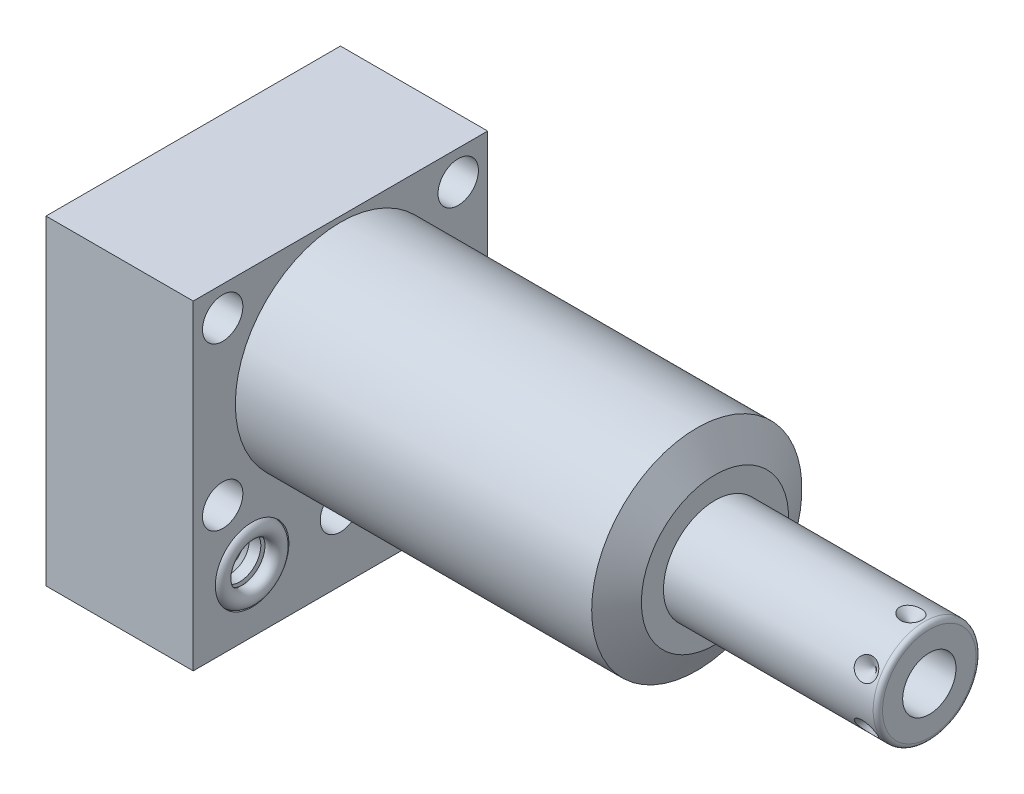
SolidWorks part; units mm, degrees
material "Alloy Steel"
ref_plane "Front Plane" through (0, 0, 0) normal (0, 0, 1) x (1, 0, 0)
ref_plane "Top Plane" through (0, 0, 0) normal (0, 1, 0) x (1, 0, 0)
ref_plane "Right Plane" through (0, 0, 0) normal (1, 0, 0) x (0, 0, -1)
ref_plane "Plane1" through (0, 0, 0) normal (1, 0, 0) x (0, 0, -1)
sketch "Sketch1" plane through (0, 0, 0) normal (1, 0, 0) x (0, 0, -1)
  line L0 (-31.75, 23.8252) -> (-31.75, -45.2628)
  line L1 (-31.75, -45.2628) -> (31.75, -45.2628)
  line L2 (31.75, -45.2628) -> (31.75, 23.8252)
  line L3 (31.75, 23.8252) -> (-31.75, 23.8252)
  line L4 (0, -55.6514) -> (0, 27.6098) construction
  dimension "D1" = 63.5
  dimension "D2" = 69.088
  dimension "D3" = 23.8252
extrude "Extrude1" add sketch "Sketch1" along normal blind 80.772 and the other way blind 31.75
ref_plane "Plane2" through (0, 0, 0) normal (1, 0, 0) x (0, 0, -1)
sketch "Sketch2" plane through (0, 0, 0) normal (1, 0, 0) x (0, 0, -1)
  line L0 (-26.0541, 0) -> (26.0541, 0) construction
  line L5 (31.75, 23.8252) -> (-31.75, 23.8252)
  line L6 (-31.75, 23.8252) -> (-31.75, -45.2628)
  line L7 (-31.75, -45.2628) -> (31.75, -45.2628)
  line L8 (31.75, -45.2628) -> (31.75, 23.8252)
  line L9 (31.75, 23.8252) -> (-31.75, 23.8252)
  line L10 (-31.75, 23.8252) -> (-31.75, -45.2628)
  line L11 (-31.75, -45.2628) -> (31.75, -45.2628)
  line L12 (31.75, -45.2628) -> (31.75, 23.8252)
  circle A0 centre (0, 0) radius 22.6695
  dimension "D1" = 45.339
  dimension "D2" = 0
extrude "Cut-Extrude1" cut sketch "Sketch2" along normal up to next
ref_plane "Plane3" through (0, 0, 0) normal (0, 0, 1) x (1, 0, 0)
sketch "Sketch3" plane through (0, 0, 0) normal (0, 0, 1) x (1, 0, 0)
  line L0 (76.8492, 22.6695) -> (80.772, 15.875)
  line L1 (76.0371, 0) -> (80.9975, 0) construction
  line L2 (80.772, 22.6695) -> (80.772, 15.875)
  line L3 (80.772, 22.6695) -> (76.8492, 22.6695)
  line L4 (80.772, 22.6695) -> (0, 22.6695) construction
  line L5 (80.772, -22.6695) -> (80.772, 22.6695) construction
  dimension "D1" = 31.75
  dimension "D2" = 30
revolve "Cut-Revolve1" cut sketch "Sketch3" angle 360 about L1
ref_plane "Plane4" through (-29.083, -31.75, 19.05) normal (0, 0, 1) x (0, 1, 0)
sketch "S2D0002" plane through (-29.083, -31.75, 19.05) normal (0, 0, 1) x (0, 1, 0)
  line L0 (0, 0) -> (4.5466, 0)
  line L1 (4.5466, 0) -> (4.1066, -2.0701)
  line L2 (4.1066, -2.0701) -> (3.4544, -2.7223)
  line L3 (3.4544, -2.7223) -> (3.4544, -13.97)
  line L4 (3.4544, -13.97) -> (0, -13.97)
  line L5 (0, -13.97) -> (0, 0)
  line L6 (0, -14.6685) -> (0, 0.6985) construction
  dimension "D1" = 13.97
revolve "Cut-Revolve2" cut sketch "S2D0002" angle 360 about L6
ref_plane "Plane5" through (-29.083, -31.75, -19.05) normal (0, 0, 1) x (0, 1, 0)
sketch "Sketch5" plane through (-29.083, -31.75, -19.05) normal (0, 0, 1) x (0, 1, 0)
  line L0 (0, 0) -> (4.5466, 0)
  line L1 (4.5466, 0) -> (4.1066, -2.0701)
  line L2 (4.1066, -2.0701) -> (3.4544, -2.7223)
  line L3 (3.4544, -2.7223) -> (3.4544, -13.97)
  line L4 (3.4544, -13.97) -> (0, -13.97)
  line L5 (0, -13.97) -> (0, 0)
  line L6 (0, -14.6685) -> (0, 0.6985) construction
  dimension "D1" = 13.97
revolve "Cut-Revolve3" cut sketch "Sketch5" angle 360 about L6
ref_plane "Plane6" through (-2.667, -31.75, 19.05) normal (0, 0, 1) x (0, -1, 0)
sketch "Sketch6" plane through (-2.667, -31.75, 19.05) normal (0, 0, 1) x (0, -1, 0)
  line L0 (0, 0) -> (4.5466, 0)
  line L1 (4.5466, 0) -> (4.1066, -2.0701)
  line L2 (4.1066, -2.0701) -> (3.4544, -2.7223)
  line L3 (3.4544, -2.7223) -> (3.4544, -12.192)
  line L4 (3.4544, -12.192) -> (0, -12.192)
  line L5 (0, -12.192) -> (0, 0)
  line L6 (0, -12.8016) -> (0, 0.6096) construction
  dimension "D1" = 12.192
revolve "Cut-Revolve4" cut sketch "Sketch6" angle 360 about L6
ref_plane "Plane7" through (-2.667, -31.75, -19.05) normal (0, 0, 1) x (0, -1, 0)
sketch "Sketch7" plane through (-2.667, -31.75, -19.05) normal (0, 0, 1) x (0, -1, 0)
  line L0 (0, 0) -> (4.5466, 0)
  line L1 (4.5466, 0) -> (4.1066, -2.0701)
  line L2 (4.1066, -2.0701) -> (3.4544, -2.7223)
  line L3 (3.4544, -2.7223) -> (3.4544, -12.192)
  line L4 (3.4544, -12.192) -> (0, -12.192)
  line L5 (0, -12.192) -> (0, 0)
  line L6 (0, -12.8016) -> (0, 0.6096) construction
  dimension "D1" = 12.192
revolve "Cut-Revolve5" cut sketch "Sketch7" angle 360 about L6
ref_plane "Plane8" through (-15.875, -51.6128, 19.05) normal (0, 0, 1) x (-1, 0, 0)
sketch "Sketch8" plane through (-15.875, -51.6128, 19.05) normal (0, 0, 1) x (-1, 0, 0)
  line L0 (0, -6.604) -> (6.1849, -6.604)
  line L1 (6.1849, -6.604) -> (5.6423, -9.1567)
  line L2 (5.6423, -9.1567) -> (4.9784, -9.8206)
  line L3 (4.9784, -9.8206) -> (4.9784, -25.654)
  line L4 (4.9784, -25.654) -> (0, -25.654)
  line L5 (0, -25.654) -> (0, -6.604)
  line L6 (0, -26.67) -> (0, 1.27) construction
  line L7 (15.875, -6.35) -> (-15.875, -6.35) construction
  dimension "D1" = 19.05
  dimension "D2" = 0.254
revolve "Cut-Revolve6" cut sketch "Sketch8" angle 360 about L6
ref_plane "Plane9" through (-15.875, -51.6128, -19.05) normal (0, 0, 1) x (-1, 0, 0)
sketch "Sketch9" plane through (-15.875, -51.6128, -19.05) normal (0, 0, 1) x (-1, 0, 0)
  line L0 (0, -6.604) -> (6.1849, -6.604)
  line L1 (6.1849, -6.604) -> (5.6423, -9.1567)
  line L2 (5.6423, -9.1567) -> (4.9784, -9.8206)
  line L3 (4.9784, -9.8206) -> (4.9784, -25.654)
  line L4 (4.9784, -25.654) -> (0, -25.654)
  line L5 (0, -25.654) -> (0, -6.604)
  line L6 (0, -26.67) -> (0, 1.27) construction
  line L7 (15.875, -6.35) -> (-15.875, -6.35) construction
  dimension "D1" = 19.05
  dimension "D2" = 0.254
revolve "Cut-Revolve7" cut sketch "Sketch9" angle 360 about L6
ref_plane "Plane10" through (0, 0, 0) normal (0, 0, 1) x (1, 0, 0)
sketch "Sketch18" plane through (0, 0, 0) normal (1, 0, 0) x (0, 0, -1)
  circle A0 centre (-19.05, -31.75) radius 7.9375
  circle A1 centre (19.05, -31.75) radius 7.9375
  dimension "D1" = 15.875
extrude "Cut-Extrude2" cut sketch "Sketch18" against normal blind 2.667
sketch "Sketch19" plane through (-31.75, 0, 0) normal (-1, 0, 0) x (0, 0, 1)
  circle A0 centre (-19.05, -31.75) radius 7.9375
  circle A1 centre (19.05, -31.75) radius 7.9375
  dimension "D1" = 15.875
extrude "Cut-Extrude3" cut sketch "Sketch19" against normal blind 2.667
sketch "Sketch20" plane through (0, -45.2628, 0) normal (0, -1, 0) x (1, 0, 0)
  circle A0 centre (-15.875, -19.05) radius 9.525
  circle A1 centre (-15.875, 19.05) radius 9.525
  circle A2 centre (-15.875, 19.05) radius 6.1849 construction
  dimension "D1" = 19.05
extrude "Cut-Extrude4" cut sketch "Sketch20" against normal blind 0.254
sketch "Sketch10" plane through (0, 0, 0) normal (0, 0, 1) x (1, 0, 0)
  line L0 (80.772, 0) -> (80.772, 11.1125)
  line L1 (80.772, 11.1125) -> (125.984, 11.1125)
  line L2 (127, 10.0965) -> (127, 0)
  line L3 (127, 0) -> (80.772, 0)
  line L4 (58.2708, 0) -> (120.537, 0) construction
  line L5 (80.772, -15.875) -> (80.772, 15.875) construction
  line L6 (-31.75, 23.8252) -> (-31.75, -45.2628) construction
  arc A0 (127, 10.0965) -> (125.984, 11.1125) centre (125.984, 10.0965) ccw
  point P0 (80.772, 0)
  dimension "D2" = 1.016
  dimension "D1" = 22.225
  dimension "D3" = 158.75
revolve "Revolve1" add sketch "Sketch10" angle 360 about L4
ref_plane "Plane11" through (118.6434, -5.7531, 0) normal (0, 0, 1) x (0, -1, 0)
sketch "S2D0001" plane through (118.6434, -5.7531, 0) normal (0, 0, 1) x (0, -1, 0)
  line L0 (0, 8.3566) -> (0, -8.6614)
  line L1 (0, -8.6614) -> (-5.7531, -12.1182)
  line L2 (0, 8.3566) -> (-5.7531, 8.3566)
  line L3 (-5.7531, 8.3566) -> (-5.7531, -12.1182)
  line L4 (-5.7531, -34.3471) -> (-5.7531, 1.0237) construction
  line L5 (4.3434, 8.3566) -> (-15.8496, 8.3566) construction
  dimension "D1" = 11.5062
  dimension "D2" = 17.018
  dimension "D3" = 59
revolve "Cut-Revolve8" cut sketch "S2D0001" angle 360 about L4
ref_plane "Plane14" through (0, -31.75, -19.05) normal (0, -1, 0) x (0, 0, -1)
sketch "Sketch14" plane through (0, -31.75, -19.05) normal (0, -1, 0) x (0, 0, -1)
  line L0 (0, -2.8435) -> (0, 1.0401) construction
  line L1 (0, -5.3893) -> (0, -12.2901) construction
  line L2 (7.9375, -2.667) -> (-7.9375, -2.667) construction
  circle A0 centre (6.1722, -0.9017) radius 1.7653
  dimension "D1" = 3.5306
  dimension "D2" = 12.3444
revolve "Revolve2" add sketch "Sketch14" angle 360 about L0
ref_plane "Plane15" through (0, -31.75, -19.05) normal (0, -1, 0) x (0, 0, -1)
sketch "Sketch15" plane through (0, -31.75, -19.05) normal (0, -1, 0) x (0, 0, -1)
  line L0 (0, -32.7901) -> (0, -28.9065) construction
  line L1 (0, -29.083) -> (0, -27.0129) construction
  line L2 (-7.9375, -29.083) -> (7.9375, -29.083) construction
  circle A0 centre (6.1722, -30.8483) radius 1.7653
  dimension "D1" = 3.5306
  dimension "D2" = 12.3444
revolve "Revolve3" add sketch "Sketch15" angle 360 about L0
ref_plane "Plane16" through (114.681, -11.1125, 0) normal (0, 0, 1) x (-1, 0, 0)
sketch "Sketch16" plane through (114.681, -11.1125, 0) normal (0, 0, 1) x (-1, 0, 0)
  line L0 (-8.3566, 0) -> (-5.9436, 0)
  line L1 (-5.9436, 0) -> (-8.3566, -2.413)
  line L2 (-8.3566, 0) -> (-8.3566, -2.413)
  line L3 (-8.3566, -5.0193) -> (-8.3566, 0.1207) construction
  line L4 (33.909, 0) -> (-11.303, 0) construction
  line L5 (-12.319, -1.016) -> (-12.319, -21.209) construction
  dimension "D1" = 3.9624
  dimension "D2" = 4.826
  dimension "D3" = 45
ref_plane "Plane17" through (114.681, 11.1125, 0) normal (0, 0, 1) x (1, 0, 0)
revolve "Cut-Revolve9" cut sketch "Sketch16" angle 360 about L3
pattern_circular "CirPattern1" count 6 over 360 of "Cut-Revolve9"
hole_wizard "Hole1" positions "Sketch22" profile "Sketch21" legacy end condition up to next
sketch "Sketch22" plane through (0, 0, 0) normal (1, 0, 0) x (0, 0, -1)
  line L0 (0, 0) -> (-38.8053, 0) construction
  line L1 (0, 0) -> (0, 31.2017) construction
  point P0 (-25.4, 17.4752)
  point P1 (0, -30.8356)
  point P12 (-25.4, -17.4752)
  point P14 (25.4, 17.4752)
  point P15 (25.4, -17.4752)
  dimension "D1" = 25.4
  dimension "D2" = 17.4752
  dimension "D3" = 30.8356
sketch "Sketch21" plane through (0, 17.4752, 25.4) normal (0, 1, 0) x (0, 0, -1)
  line L0 (0, 0) -> (0, 31.75)
  line L1 (0, 31.75) -> (4.3561, 31.75)
  line L2 (4.3561, 31.75) -> (4.3561, 0)
  line L3 (4.3561, 0) -> (0, 0)
  line L4 (0, 110) -> (0, -10) construction
  dimension "Diameter" = 8.7122
  dimension "Depth" = 31.75
pattern_linear "LPattern1" count 2 spacing 38.1 along (0, 0, 1) of "Revolve2", "Revolve3"
